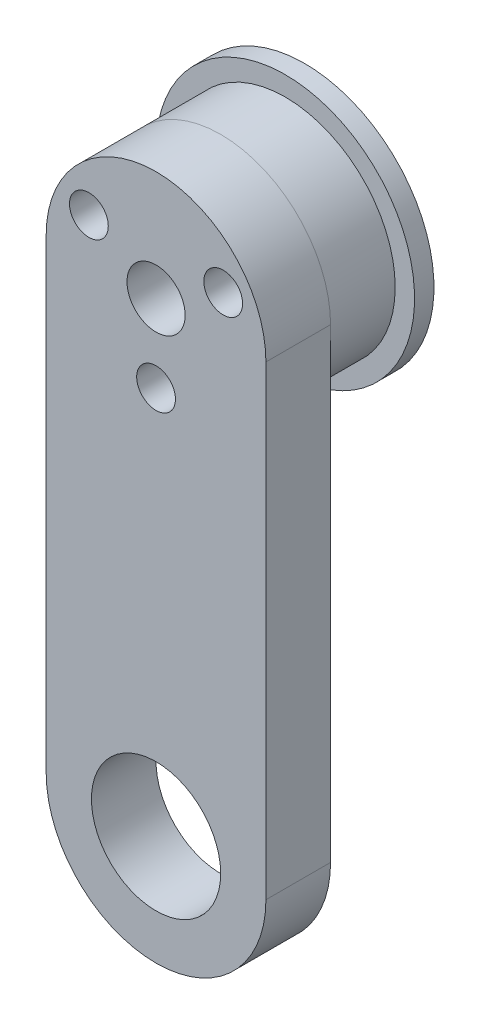
SolidWorks part; units mm, degrees
material "Thornel Mat VMA"
ref_plane "前视基准面" through (0, 0, 0) normal (0, 0, 1) x (1, 0, 0)
ref_plane "上视基准面" through (0, 0, 0) normal (0, 1, 0) x (1, 0, 0)
ref_plane "右视基准面" through (0, 0, 0) normal (1, 0, 0) x (0, 0, -1)
sketch "草图1" plane through (0, 0, 0) normal (0, 0, 1) x (1, 0, 0)
  line L0 (0, 0) -> (0, -36.0299) construction
  line L1 (-8.5, -36.0299) -> (-8.5, 0)
  line L2 (8.5, -36.0299) -> (8.5, 0)
  arc A0 (8.5, 0) -> (-8.5, 0) centre (0, 0) ccw
  arc A1 (-8.5, -36.0299) -> (8.5, -36.0299) centre (0, -36.0299) ccw
  circle A2 centre (-5.1962, 3) radius 1.5
  circle A5 centre (0, 0) radius 2.25
  circle A6 centre (0, -36.0299) radius 5
  circle A8 centre (0, 0) radius 6 construction
  circle A16 centre (5.1962, 3) radius 1.5
  circle A17 centre (0, -6) radius 1.5
  dimension "D2" = 17
  dimension "D4" = 3
  dimension "D7" = 4.5
  dimension "D8" = 10
  dimension "D9" = 3
  dimension "D6" = 2.5
  dimension "D5" = 12
  dimension "D3" = 36.0299
extrude "凸台-拉伸1" add sketch "草图1" along normal blind 5
sketch "草图2" plane through (0, 0, 0) normal (0, 0, -1) x (-1, 0, 0)
  arc A0 (8.5, 0) -> (-8.5, 0) centre (0, 0) ccw construction
  circle A1 centre (0, 0) radius 8.5
  circle A2 centre (0, -6) radius 1.5 construction
  circle A3 centre (5.1962, 3) radius 1.5 construction
  circle A5 centre (-5.1962, 3) radius 1.5 construction
  circle A6 centre (0, -6) radius 1.5
  circle A7 centre (5.1962, 3) radius 1.5
  circle A8 centre (0, 0) radius 3.35
  circle A9 centre (-5.1962, 3) radius 1.5
  dimension "D1" = 6.7
extrude "凸台-拉伸2" add sketch "草图2" along normal blind 5 separate body
sketch "草图3" plane through (0, 0, -5) normal (0, 0, -1) x (-1, 0, 0)
  circle A0 centre (0, 0) radius 8.5 construction
  circle A1 centre (-5.1962, 3) radius 1.5
  circle A2 centre (-5.1962, 3) radius 1.5
  circle A3 centre (0, 0) radius 3.35
  circle A4 centre (0, 0) radius 3.35
  circle A5 centre (5.1962, 3) radius 1.5
  circle A6 centre (5.1962, 3) radius 1.5
  circle A7 centre (0, -6) radius 1.5
  circle A8 centre (0, -6) radius 1.5
  circle A10 centre (0, 0) radius 10
  dimension "D5" = 1.5
  dimension "D1" = 0
  dimension "D2" = 0
  dimension "D3" = 0
  dimension "D4" = 0
extrude "凸台-拉伸3" add sketch "草图3" along normal blind 1.5 separate body
